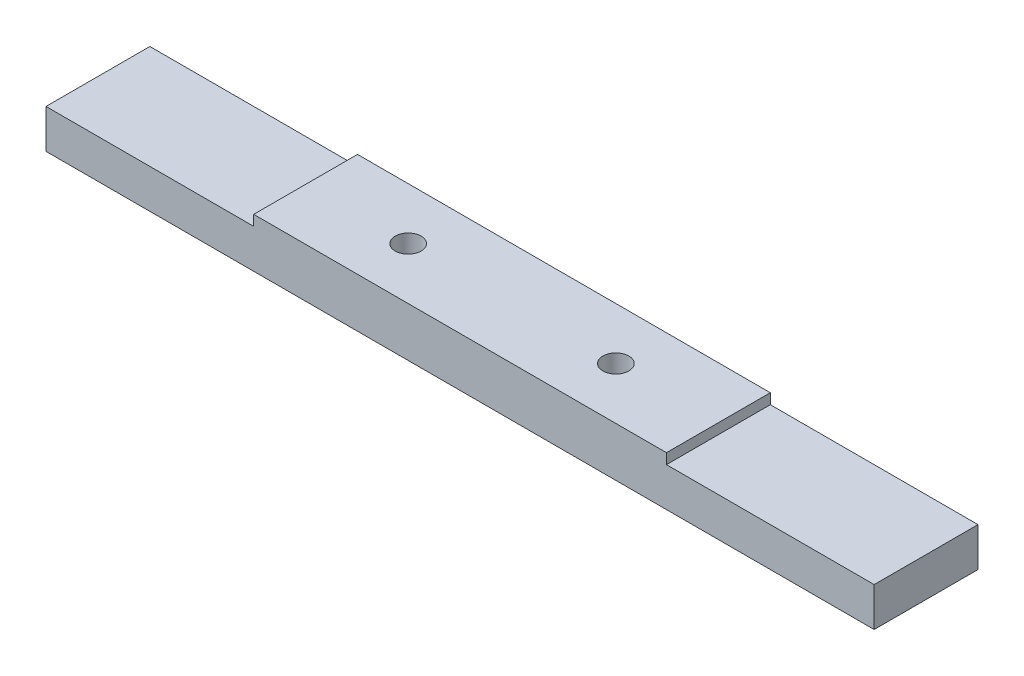
SolidWorks part; units mm, degrees
material "3.1325 (EN-AW 2017A)"
ref_plane "Ebene vorne" through (0, 0, 0) normal (0, 0, 1) x (1, 0, 0)
ref_plane "Ebene oben" through (0, 0, 0) normal (0, 1, 0) x (1, 0, 0)
ref_plane "Ebene rechts" through (0, 0, 0) normal (1, 0, 0) x (0, 0, -1)
sketch "Skizze1" plane through (0, 0, 0) normal (0, 0, 1) x (1, 0, 0)
  line L0 (-31.9, 0) -> (-15.9, 0)
  line L1 (-15.9, 0) -> (-15.9, 0.8)
  line L2 (-15.9, 0.8) -> (15.9, 0.8)
  line L3 (15.9, 0.8) -> (15.9, 0)
  line L4 (15.9, 0) -> (31.9, 0)
  line L5 (31.9, 0) -> (31.9, -3)
  line L6 (31.9, -3) -> (-31.9, -3)
  line L7 (-31.9, -3) -> (-31.9, 0)
  line L8 (-15.9, 0) -> (15.9, 0) construction
  line L9 (0, 0.8) -> (0, -3) construction
  dimension "D1" = 0.8
  dimension "D2" = 31.8
  dimension "D3" = 63.8
  dimension "D4" = 3
extrude "Aufsatz-Linear austragen1" add sketch "Skizze1" along normal mid plane 8
hole_wizard "Formsenkung für M3 Senkschraube mit Innensechskant1" positions "Skizze3" profile "Skizze2" countersink size "M3" standard "DIN" end condition through all
sketch "Skizze3" plane through (0, -3, 0) normal (0, -1, 0) x (-1, 0, 0)
  line L0 (8, 0) -> (0, 0) construction
  line L1 (0, 0) -> (-8, 0) construction
  point P0 (8, 0)
  point P2 (-8, 0)
  dimension "D1" = 8
sketch "Skizze2" plane through (-8, -3, 0) normal (1, 0, 0) x (0, 0, -1)
  line L0 (0, 0) -> (0, 3.8)
  line L1 (0, 3.8) -> (1, 3.8)
  line L2 (1, 3.8) -> (1, 0.75)
  line L3 (1, 0.75) -> (1.75, 0)
  line L5 (1.75, 0) -> (0, 0)
  line L6 (-1, 0.75) -> (-1.75, 0) construction
  line L11 (0, -6.35) -> (0, 107.95) construction
  dimension "Bohrerdurchmesser" = 2
  dimension "Bohrungstiefe" = 3.8
  dimension "Senkdurchmesser (Oben)" = 3.5
  dimension "Senkwinkel (Oben)" = 90
